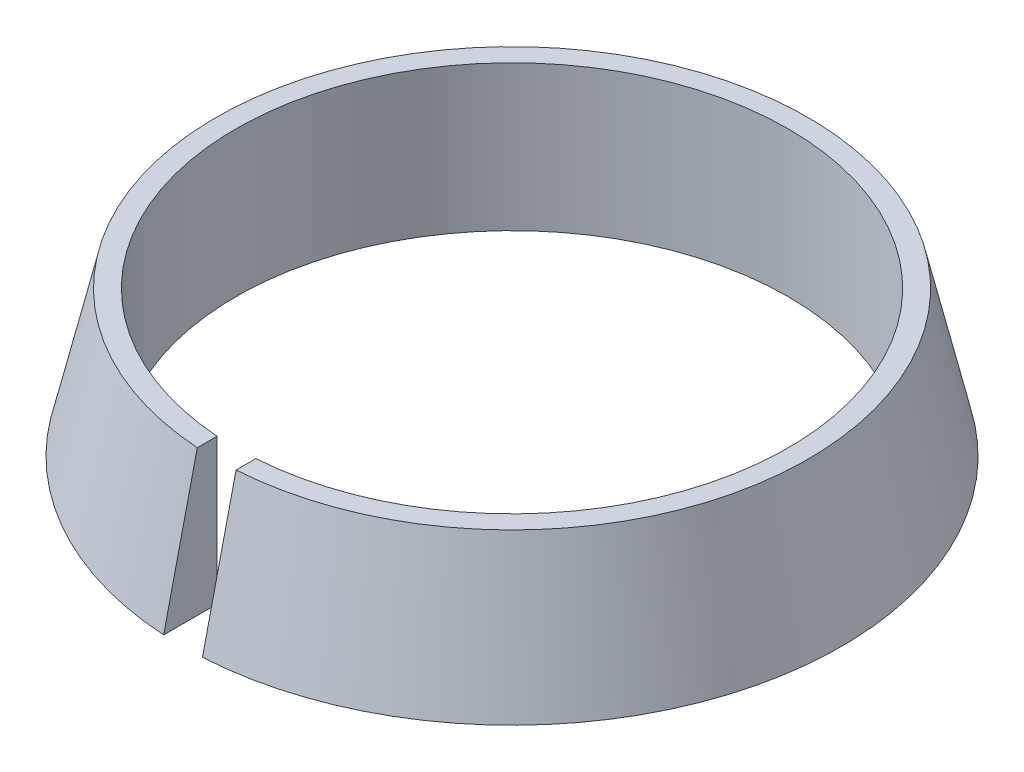
SolidWorks part; units mm, degrees
ref_plane "Plan de face" through (0, 0, 0) normal (0, 0, 1) x (1, 0, 0)
ref_plane "Plan de dessus" through (0, 0, 0) normal (0, 1, 0) x (1, 0, 0)
ref_plane "Plan de droite" through (0, 0, 0) normal (1, 0, 0) x (0, 0, -1)
sketch "Esquisse1" plane through (0, 0, 0) normal (0, 0, 1) x (1, 0, 0)
  line L0 (0, -11.2329) -> (0, 27.987) construction
  line L1 (14.25, 0) -> (14.25, 7.5)
  line L2 (14.25, 0) -> (17, 0)
  line L3 (17, 0) -> (15.2685, 7.5)
  line L4 (15.2685, 7.5) -> (14.25, 7.5)
  dimension "D1" = 28.5
  dimension "D2" = 34
  dimension "D3" = 7.5
  dimension "D4" = 13
revolve "Révolution1" add sketch "Esquisse1" angle 360 about L0
sketch "Esquisse2" plane through (0, 0, 0) normal (0, 0, 1) x (1, 0, 0)
  line L0 (15.2685, 7.5) -> (-15.2685, 7.5) construction
  line L1 (-1, 0) -> (1, 0)
  line L2 (-1, 0) -> (-1, 7.5)
  line L3 (-1, 7.5) -> (1, 7.5)
  line L4 (1, 0) -> (1, 7.5)
  dimension "D1" = 2
extrude "Enlèv. mat.-Extru.4" cut sketch "Esquisse2" along normal through all
